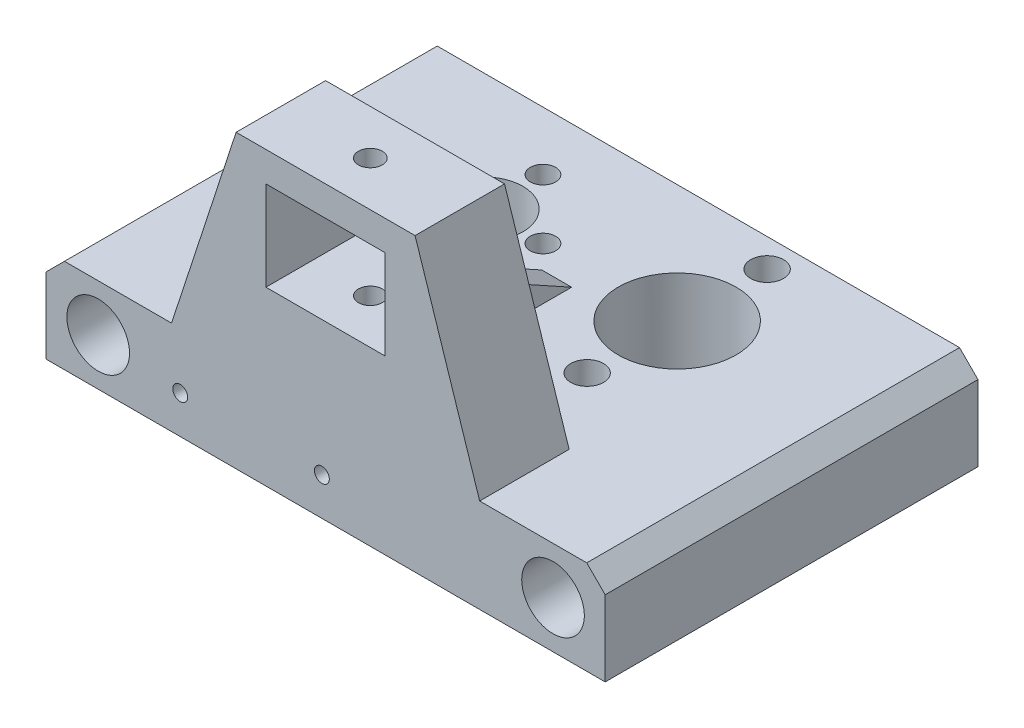
SolidWorks part; units mm, degrees
ref_plane "Front Plane" through (0, 0, 0) normal (0, 0, 1) x (1, 0, 0)
ref_plane "Top Plane" through (0, 0, 0) normal (0, 1, 0) x (1, 0, 0)
ref_plane "Right Plane" through (0, 0, 0) normal (1, 0, 0) x (0, 0, -1)
sketch "Sketch1" plane through (0, 0, 0) normal (0, 1, 0) x (1, 0, 0)
  line L0 (0, 34.15) -> (75, 34.15) construction
  line L1 (0, 0) -> (75, 0)
  line L2 (0, 0) -> (0, 50)
  line L3 (0, 50) -> (75, 50)
  line L4 (75, 0) -> (75, 50)
  line L5 (37.5, 50) -> (37.5, 0) construction
  line L6 (37.5, 34.15) -> (24.5, 34.15) construction
  line L7 (37.5, 34.15) -> (50.5, 34.15) construction
  circle A0 centre (24.5, 34.15) radius 5.3
  circle A1 centre (50.5, 34.15) radius 7.9
  point P15 (37.5, 34.15)
  dimension "D2" = 10.6
  dimension "D6" = 15.8
  dimension "D1" = 26
  dimension "D3" = 75
  dimension "D4" = 50
  dimension "D5" = 15.85
extrude "Boss-Extrude1" add sketch "Sketch1" along normal blind 0.1
sketch "Sketch2" plane through (0, 0.1, 0) normal (0, 1, 0) x (1, 0, 0)
  line L4 (0, 50) -> (12.5, 50)
  line L5 (0, 50) -> (0, 10)
  line L6 (0, 10) -> (12.5, 10)
  line L7 (12.5, 50) -> (12.5, 10)
  line L8 (75, 50) -> (62.5, 50)
  line L9 (75, 50) -> (75, 10)
  line L10 (75, 10) -> (62.5, 10)
  line L11 (62.5, 50) -> (62.5, 10)
  dimension "D1" = 40
  dimension "D3" = 12.5
extrude "Boss-Extrude2" add sketch "Sketch2" along normal blind 12.5
sketch "Sketch4" plane through (0, 0.1, 0) normal (0, 1, 0) x (1, 0, 0)
  line L0 (37.5, 0) -> (37.5, 50) construction
  line L1 (0, 0) -> (75, 0) construction
  line L2 (62.5, 50) -> (12.5, 50) construction
  line L4 (45.5, 0) -> (49.5, 0)
  line L5 (45.5, 0) -> (45.5, 12)
  line L6 (45.5, 12) -> (49.5, 12)
  line L7 (49.5, 0) -> (49.5, 12)
  line L8 (25.5, 0) -> (29.5, 0)
  line L9 (25.5, 0) -> (25.5, 12)
  line L10 (25.5, 12) -> (29.5, 12)
  line L11 (29.5, 0) -> (29.5, 12)
  dimension "D1" = 4
  dimension "D3" = 8
  dimension "D4" = 8
  dimension "D5" = 12
extrude "Boss-Extrude3" add sketch "Sketch4" along normal blind 35
sketch "Sketch5" plane through (0, 0, -12) normal (0, 0, -1) x (-1, 0, 0)
  line L0 (-49.5, 0.1) -> (-45.5, 0.1) construction
  line L1 (-49.5, 35.1) -> (-25.5, 35.1)
  line L2 (-49.5, 35.1) -> (-49.5, 39.1)
  line L3 (-49.5, 39.1) -> (-25.5, 39.1)
  line L4 (-25.5, 35.1) -> (-25.5, 39.1)
extrude "Boss-Extrude4" add sketch "Sketch5" against normal up to surface (12 mm away) up to face at (37.5, 11.75, 0)
sketch "Sketch7" plane through (0, 0.1, 0) normal (0, 1, 0) x (1, 0, 0)
  line L0 (50.5, 26.25) -> (50.5, 42.05) construction
  line L1 (24.5, 39.45) -> (24.5, 28.85) construction
  line L2 (29.8, 34.15) -> (19.2, 34.15) construction
  circle A1 centre (50.5, 22.08) radius 2.2
  circle A2 centre (50.5, 46.215) radius 2.2
  circle A3 centre (50.5, 34.15) radius 7.9 construction
  circle A4 centre (24.5, 34.15) radius 5.3 construction
  circle A6 centre (24.5, 42.15) radius 1.7
  circle A7 centre (16.5, 34.15) radius 1.7
  circle A8 centre (32.5, 34.15) radius 1.7
  circle A9 centre (24.5, 26.15) radius 1.7
  point P10 (50.5, 34.15)
  point P20 (24.5, 34.15)
  dimension "D3" = 4.4
  dimension "D6" = 3.4
  dimension "D1" = 12.065
  dimension "D2" = 12.07
  dimension "D4" = 8
  dimension "D5" = 8
extrude "Cut-Extrude4" cut sketch "Sketch7" against normal through all
sketch "Sketch8" plane through (0, 0.1, 0) normal (0, 1, 0) x (1, 0, 0)
  line L1 (45.5, 0) -> (29.5, 0)
  line L2 (45.5, 0) -> (45.5, 12)
  line L3 (45.5, 12) -> (29.5, 12)
  line L4 (29.5, 0) -> (29.5, 12)
extrude "Boss-Extrude5" add sketch "Sketch8" along normal blind 23
sketch "Sketch9" plane through (0, 0, 0) normal (0, 0, 1) x (1, 0, 0)
  line L0 (49.5, 39.1) -> (62.25, 0.1)
  line L1 (49.5, 0.1) -> (75, 0.1) construction
  line L2 (62.25, 0.1) -> (49.5, 0.1)
  line L3 (49.5, 0.1) -> (49.5, 39.1)
  line L4 (37.5, 23.1) -> (37.5, 35.1) construction
  line L5 (29.5, 23.1) -> (45.5, 23.1) construction
  line L6 (29.5, 35.1) -> (45.5, 35.1) construction
  line L7 (12.75, 0.1) -> (25.5, 0.1)
  line L8 (25.5, 39.1) -> (12.75, 0.1)
  line L9 (25.5, 0.1) -> (25.5, 39.1)
extrude "Boss-Extrude6" add sketch "Sketch9" against normal up to surface (12 mm away) up to face at (37.5, 19.6, -12)
sketch "Sketch6" plane through (0, 39.1, 0) normal (0, 1, 0) x (1, 0, 0)
  line L0 (49.5, 6) -> (25.5, 6) construction
  line L3 (37.5, 0) -> (37.5, 12) construction
  line L4 (49.5, 0) -> (25.5, 0) construction
  line L5 (25.5, 12) -> (49.5, 12) construction
  line L6 (25.5, 0) -> (25.5, 12) construction
  line L7 (49.5, 0) -> (49.5, 12) construction
  circle A0 centre (37.5, 6) radius 1.6
  dimension "D1" = 3.2
extrude "Cut-Extrude2" cut sketch "Sketch6" against normal blind 25
sketch "Sketch10" plane through (0, 0.1, 0) normal (0, 1, 0) x (1, 0, 0)
  line L0 (62.25, 12) -> (12.75, 12) construction
  line L1 (39.5, 12) -> (35.5, 12)
  line L2 (39.5, 12) -> (39.5, 50)
  line L3 (39.5, 50) -> (35.5, 50)
  line L4 (35.5, 12) -> (35.5, 50)
  line L5 (37.5, 12) -> (37.5, 50) construction
  line L6 (62.5, 50) -> (12.5, 50) construction
  point P6 (37.5, 50)
  dimension "D1" = 4
extrude "Boss-Extrude7" add sketch "Sketch10" along normal blind 2
sketch "Sketch11" plane through (39.5, 0, 0) normal (1, 0, 0) x (0, 0, -1)
  line L0 (50, 2.1) -> (12, 2.1)
  line L1 (12, 2.1) -> (12, 23.1)
  line L2 (12, 23.1) -> (50, 2.1)
extrude "Boss-Extrude8" add sketch "Sketch11" against normal up to surface (4 mm away) up to face at (35.5, 1.1, -31)
sketch "Sketch12" plane through (0, 0.1, 0) normal (0, 1, 0) x (1, 0, 0)
  line L1 (39.5, 12) -> (44.5, 12)
  line L2 (39.5, 12) -> (39.5, 16.6)
  line L3 (39.5, 16.6) -> (44.5, 16.6)
  line L4 (44.5, 12) -> (44.5, 16.6)
  line L5 (35.5, 12) -> (30.5, 12)
  line L6 (35.5, 12) -> (35.5, 16.6)
  line L7 (35.5, 16.6) -> (30.5, 16.6)
  line L8 (30.5, 12) -> (30.5, 16.6)
  dimension "D1" = 5
  dimension "D2" = 4.6
revolve "Revolve1" add sketch "Sketch12" angle 90 about L1
sketch "Sketch14" plane through (0, 0.1, 0) normal (0, 1, 0) x (1, 0, 0)
  line L1 (75, 0) -> (0, 0)
  line L2 (75, 0) -> (75, 10)
  line L3 (75, 10) -> (0, 10)
  line L4 (0, 0) -> (0, 10)
  line L5 (62.5, 10) -> (12.5, 10)
  line L6 (62.5, 10) -> (62.5, 50)
  line L7 (62.5, 50) -> (12.5, 50)
  line L8 (12.5, 10) -> (12.5, 50)
  circle A0 centre (50.5, 22.08) radius 2.2
  circle A1 centre (50.5, 22.08) radius 2.2 construction
  circle A2 centre (50.5, 34.15) radius 7.9
  circle A3 centre (50.5, 46.215) radius 2.2
  circle A4 centre (32.5, 34.15) radius 1.7
  circle A5 centre (24.5, 34.15) radius 5.3
  circle A6 centre (16.5, 34.15) radius 1.7
  circle A7 centre (24.5, 26.15) radius 1.7
  circle A8 centre (24.5, 42.15) radius 1.7
  circle A9 centre (24.5, 42.15) radius 1.7 construction
  circle A10 centre (24.5, 34.15) radius 5.3 construction
  circle A11 centre (50.5, 46.215) radius 2.2 construction
  circle A12 centre (50.5, 34.15) radius 7.9 construction
  circle M8 centre (50.5, 22.08) radius 2.2
  circle M9 centre (50.5, 46.215) radius 2.2
  circle M10 centre (50.5, 34.15) radius 7.9
  line M11 (39.5, 50) -> (39.5, 16.6)
  line M12 (39.5, 16.6) -> (44.5, 16.6)
  line M13 (44.5, 16.6) -> (44.5, 12)
  line M14 (44.5, 12) -> (62.25, 12)
  line M15 (62.25, 12) -> (62.25, 0)
  line M16 (62.25, 0) -> (75, 0)
  line M17 (75, 0) -> (75, 10)
  line M18 (75, 10) -> (62.5, 10)
  line M19 (62.5, 10) -> (62.5, 50)
  line M20 (62.5, 50) -> (39.5, 50)
extrude "Boss-Extrude9" add sketch "Sketch14" along normal up to surface (12.5 mm away) contours L3 M19 M20 M11 M12 M13 M14 M15 M9 M10 M8 | L3 M18 M15 M16 M17 | L8 L3 L7 A8 A7 A6 A5 A4 M15 M14 M13 M12 M11 | L4 L1 L3 M15 up to face at (68.75, 12.6, -30)
sketch "Sketch3" plane through (0, 0, -50) normal (0, 0, -1) x (-1, 0, 0)
  line L0 (-37.5, 0) -> (-37.5, 50000) construction
  line L1 (-75, 0) -> (0, 0) construction
  line L3 (-72.5251, 12.6) -> (-75, 12.6)
  line L4 (-75, 12.6) -> (0, 12.6) construction
  line L5 (-75, 12.6) -> (-75, 10.1251)
  line L6 (-75, 12.6) -> (-75, 0) construction
  line L7 (-75, 10.1251) -> (-72.5251, 12.6)
  line L12 (-37.5, 12.6) -> (-37.5, 0) construction
  line L13 (-61, 6.3) -> (-75, 6.3) construction
  line L14 (-14, 6.3) -> (0, 6.3) construction
  line L15 (-37.5, 12.6) -> (-37.5, 0) construction
  line L19 (0, 10.1251) -> (-2.4749, 12.6)
  line L20 (0, 12.6) -> (0, 10.1251)
  line L21 (-2.4749, 12.6) -> (0, 12.6)
  line L22 (-75, 12.6) -> (-75, 0) construction
  circle A0 centre (-68, 6.3) radius 4.2
  circle A1 centre (-7, 6.3) radius 4.2
  point P4 (-37.5, 0)
  dimension "D1" = 8.4
  dimension "D2" = 3.5
  dimension "D3" = 14
extrude "Cut-Extrude1" cut sketch "Sketch3" against normal through all
sketch "Sketch15" plane through (0, 0, 0) normal (0, 0, 1) x (1, 0, 0)
  line L0 (0, 5.0626) -> (75, 5.0626) construction
  line L1 (0, 10.1251) -> (0, 0) construction
  line L2 (75, 10.1251) -> (75, 0) construction
  line L3 (37.5, 39.1) -> (37.5, 0) construction
  line L4 (49.5, 39.1) -> (25.5, 39.1) construction
  line L5 (0, 0) -> (75, 0) construction
  circle A0 centre (18, 5.0626) radius 1
  circle A1 centre (37, 5.0626) radius 1
  dimension "D3" = 2
  dimension "D1" = 19
  dimension "D2" = 0.5
extrude "Cut-Extrude5" cut sketch "Sketch15" against normal blind 8
equation "\"8mm hole\" = 8.4mm"
equation "\"22mm hole\"= 23mm"
equation "\"15mm hole\"= 15.8mm"
equation "\"D6@Sketch1\"= \"15mm hole\""
equation "\"D1@Sketch3\"= \"8mm hole\""
equation "\"bed height offset\"= 3mm"
